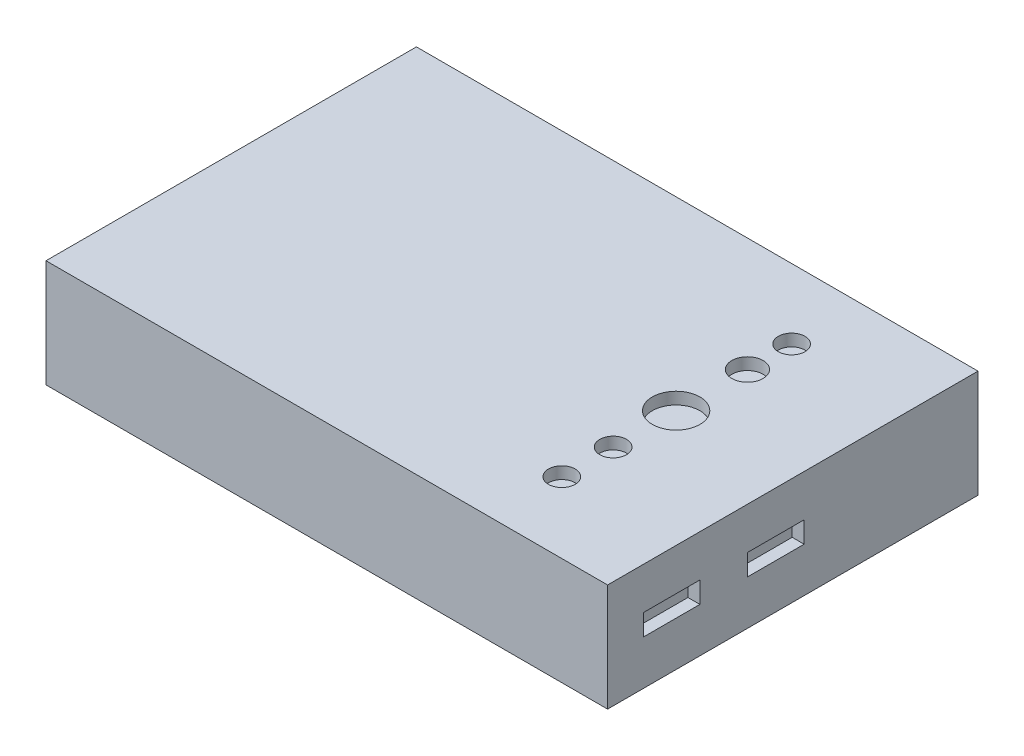
SolidWorks part; units mm, degrees
material "PE Low/Medium Density"
ref_plane "Front Plane" through (0, 0, 0) normal (0, 0, 1) x (1, 0, 0)
ref_plane "Top Plane" through (0, 0, 0) normal (0, 1, 0) x (1, 0, 0)
ref_plane "Right Plane" through (0, 0, 0) normal (1, 0, 0) x (0, 0, -1)
sketch "Sketch1" plane through (0, 0, 0) normal (0, 1, 0) x (1, 0, 0)
  line L1 (0, 0) -> (119.38, 0)
  line L2 (0, 0) -> (0, 78.74)
  line L3 (0, 78.74) -> (119.38, 78.74)
  line L4 (119.38, 0) -> (119.38, 78.74)
  dimension "D1" = 119.38
  dimension "D2" = 78.74
extrude "Boss-Extrude1" add sketch "Sketch1" along normal blind 22.86
sketch "Sketch2" plane through (119.38, 0, 0) normal (1, 0, 0) x (0, 0, -1)
  line L0 (29.78, 13.97) -> (41.78, 13.97)
  line L1 (7.62, 13.97) -> (19.62, 13.97)
  line L2 (7.62, 13.97) -> (7.62, 9.47)
  line L3 (7.62, 9.47) -> (19.62, 9.47)
  line L4 (19.62, 13.97) -> (19.62, 9.47)
  line L5 (29.78, 13.97) -> (29.78, 9.47)
  line L6 (29.78, 9.47) -> (41.78, 9.47)
  line L7 (41.78, 13.97) -> (41.78, 9.47)
  line L8 (0, 22.86) -> (0, 0) construction
  line L9 (0, 22.86) -> (78.74, 22.86) construction
  dimension "D1" = 12
  dimension "D2" = 4.5
  dimension "D3" = 7.62
  dimension "D4" = 10.16
  dimension "D5" = 8.89
extrude "Cut-Extrude1" cut sketch "Sketch2" against normal blind 2.54
sketch "Sketch3" plane through (0, 22.86, 0) normal (0, 1, 0) x (1, 0, 0)
  circle A0 centre (94.5792, 39.37) radius 5.0653
  circle A1 centre (94.5792, 54.531) radius 3.3205
  circle A2 centre (94.5792, 63.9193) radius 2.8369
  circle A3 centre (94.5792, 25.9852) radius 2.8369
  circle A4 centre (94.5792, 15.0744) radius 2.8369
  point P6 (94.5792, 63.9193)
  point P9 (94.5792, 25.9852)
  point P12 (94.5792, 15.0744)
extrude "Cut-Extrude2" cut sketch "Sketch3" against normal blind 2.54
